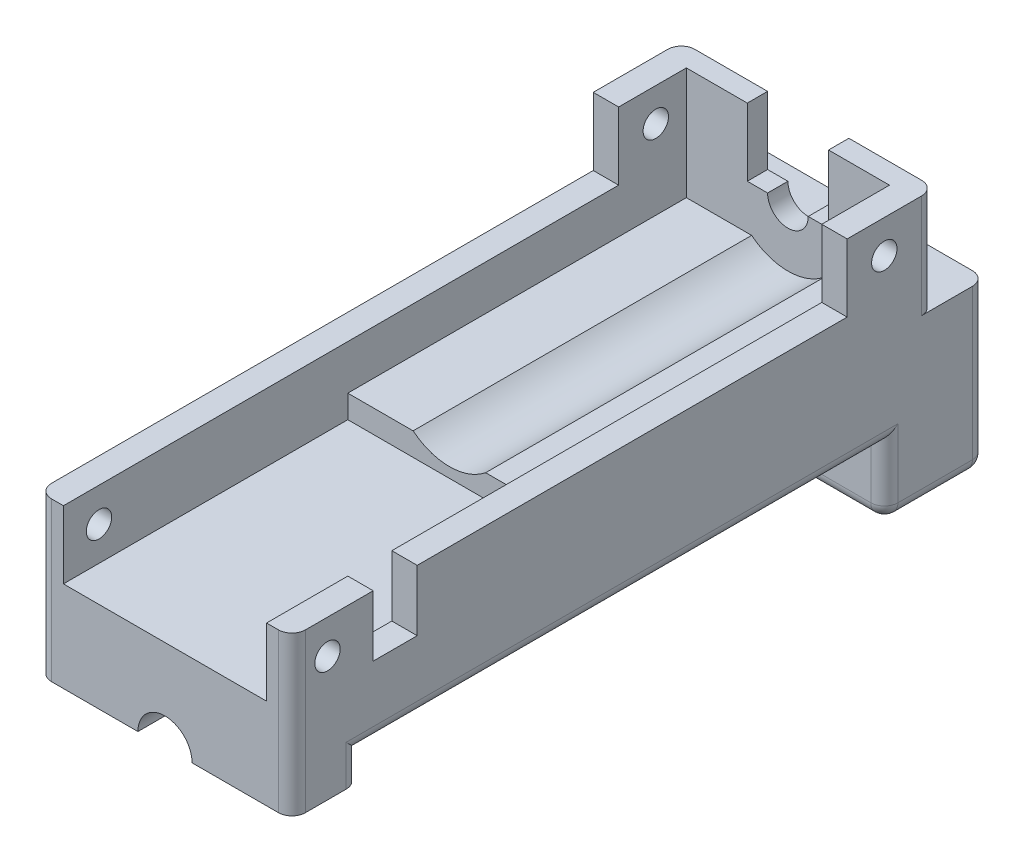
SolidWorks part; units mm, degrees
ref_plane "Front Plane" through (0, 0, 0) normal (0, 0, 1) x (1, 0, 0)
ref_plane "Top Plane" through (0, 0, 0) normal (0, 1, 0) x (1, 0, 0)
ref_plane "Right Plane" through (0, 0, 0) normal (1, 0, 0) x (0, 0, -1)
sketch "Sketch2" plane through (0, 0, 0) normal (0, 1, 0) x (1, 0, 0)
  line L1 (0, 0) -> (37.5, 0)
  line L2 (0, 0) -> (0, 95)
  line L3 (0, 95) -> (37.5, 95)
  line L4 (37.5, 0) -> (37.5, 95)
  dimension "D1" = 37.5
  dimension "D2" = 95
extrude "Boss-Extrude1" add sketch "Sketch2" along normal blind 15
sketch "Sketch3" plane through (0, 15, 0) normal (0, 1, 0) x (1, 0, 0)
  line L0 (0, 0) -> (37.5, 0) construction
  line L1 (3.75, 0) -> (33.75, 0)
  line L2 (3.75, 0) -> (3.75, 42)
  line L3 (3.75, 42) -> (33.75, 42)
  line L4 (33.75, 0) -> (33.75, 42)
  point P4 (18.75, 0)
  point P7 (18.75, 0)
  dimension "D1" = 30
  dimension "D2" = 0
  dimension "D3" = 42
extrude "Cut-Extrude1" cut sketch "Sketch3" against normal blind 10
sketch "Sketch5" plane through (0, 0, -42) normal (0, 0, 1) x (1, 0, 0)
  line L0 (33.75, 5) -> (33.75, 15) construction
  line L1 (3.75, 15) -> (33.75, 15)
  line L2 (3.75, 15) -> (3.75, 8.4)
  line L3 (3.75, 8.4) -> (33.75, 8.4)
  line L4 (33.75, 15) -> (33.75, 8.4)
  line L6 (33.75, 5) -> (3.75, 5) construction
  line L7 (33.75, 15) -> (3.75, 15) construction
  circle A0 centre (18.75, 15) radius 8.5
  line M8 (3.75, 5) -> (33.75, 5)
  dimension "D3" = 17
  dimension "D1" = 0
  dimension "D2" = 3.4
extrude "Cut-Extrude2" cut sketch "Sketch5" against normal blind 50 contours A0 L3 M8 | A0 M8 | A0 L2 L3 M8 | L3 A0 | A0 L3 L4 M8
sketch "Sketch6" plane through (0, 0, -95) normal (0, 0, -1) x (-1, 0, 0)
  line L0 (-37.5, 15) -> (0, 15) construction
  line L1 (-21.75, 15) -> (-15.75, 15)
  arc A0 (-15.75, 15) -> (-21.75, 15) centre (-18.75, 15) cw
  dimension "D1" = 3
extrude "Cut-Extrude3" cut sketch "Sketch6" against normal blind 10
chamfer "Chamfer1" [suppressed] distance 2 angle 45
sketch "Sketch7" plane through (37.5, 0, 0) normal (-1, 0, 0) x (0, 0, 1)
  line L0 (-95, 15) -> (0, 15) construction
  line L1 (-12, 15) -> (-18.5, 15)
  line L2 (-12, 15) -> (-12, 6)
  line L3 (-12, 6) -> (-18.5, 6)
  line L4 (-18.5, 15) -> (-18.5, 6)
  line L5 (-95, 15) -> (-95, 0) construction
  dimension "D1" = 76.5
  dimension "D2" = 6.5
  dimension "D3" = 9
extrude "Cut-Extrude4" cut sketch "Sketch7" against normal up to surface (33.75 mm away)
ref_plane "Plane1" through (18.75, 0, 0) normal (-1, 0, 0) x (0, 0, 1)
sketch "Sketch8" plane through (0, 15, 0) normal (0, 1, 0) x (1, 0, 0)
  line L0 (15.75, 92) -> (3.75, 92) construction
  line L1 (0, 92) -> (12.75, 92)
  line L2 (0, 92) -> (0, 95)
  line L3 (0, 95) -> (12.75, 95)
  line L4 (12.75, 92) -> (12.75, 95)
  line L5 (15.75, 95) -> (0, 95) construction
  line L6 (0, 95) -> (0, 0) construction
  line L7 (15.75, 92) -> (15.75, 95) construction
  dimension "D1" = 0
  dimension "D2" = 3
extrude "Boss-Extrude2" add sketch "Sketch8" along normal blind 10
sketch "Sketch9" plane through (0, 0, -95) normal (0, 0, -1) x (-1, 0, 0)
  line L0 (-12.75, 21.2385) -> (0, 21.2385) construction
  line L1 (-12.75, 25) -> (-12.75, 15) construction
  line L2 (0, 25) -> (0, 0) construction
  point P7 (-7.9314, 21.2385)
hole_wizard "Ø2.5mm Dowel Hole1" [suppressed] positions "Sketch10" profile "Sketch11" hole size "Ø2.5" standard "ANSI Metric"
sketch "Sketch10" plane through (0, 0, -95) normal (0, 0, -1) x (-1, 0, 0)
  point P3 (-7.5318, 21.5512)
sketch "Sketch11" plane through (7.5318, 21.5512, -95) normal (1, 0, 0) x (0, 1, 0)
  line L0 (0, 0) -> (0, 3.9013)
  line L1 (0, 3.9013) -> (1.5, 3)
  line L2 (1.5, 3) -> (1.5, 0)
  line L5 (1.5, 0) -> (0, 0)
  line L10 (0, 3.9013) -> (-1.5, 3) construction
  line L11 (0, -6.35) -> (0, 107.95) construction
  dimension "Hole Dia." = 3
  dimension "Hole Depth" = 3
  dimension "Drill Angle" = 118
mirror "Mirror1" about plane through (18.75, 0, 0) normal (-1, 0, 0) of "Boss-Extrude2", "Ø2.5mm Dowel Hole1"
hole_wizard "Ø2.5mm Dowel Hole2" positions "Sketch12" profile "Sketch13" hole size "Ø2.5" standard "ANSI Metric" end condition through all
sketch "Sketch12" plane through (37.5, 0, 0) normal (1, 0, 0) x (0, 0, -1)
  line L0 (0, 15) -> (0, 0) construction
  line L1 (0, 15) -> (12, 15) construction
  point P0 (5.25, 10)
  dimension "D1" = 5.25
  dimension "D2" = 5
sketch "Sketch13" plane through (37.5, 10, -5.25) normal (0, 1, 0) x (0, 0, -1)
  line L0 (0, 0) -> (0, 37.5)
  line L1 (0, 37.5) -> (1.875, 37.5)
  line L2 (1.875, 37.5) -> (1.875, 0)
  line L5 (1.875, 0) -> (0, 0)
  line L11 (0, -6.35) -> (0, 107.95) construction
  dimension "Thru Hole Dia." = 3.75
  dimension "Thru Hole Depth" = 37.5
sketch "Sketch14" plane through (0, 0, 0) normal (0, -1, 0) x (1, 0, 0)
  line L0 (37.5, 0) -> (37.5, -95) construction
  line L1 (0, -102.5) -> (37.5, -102.5)
  line L2 (0, -102.5) -> (0, -87.5)
  line L3 (0, -87.5) -> (37.5, -87.5)
  line L4 (37.5, -102.5) -> (37.5, -87.5)
  line L5 (37.5, -95) -> (0, -95) construction
  dimension "D1" = 7.5
  dimension "D2" = 15
extrude "Boss-Extrude3" add sketch "Sketch14" along normal blind 14.5
sketch "Sketch15" plane through (0, -14.5, 0) normal (0, -1, 0) x (1, 0, 0)
  line L0 (16.1435, -102.5) -> (16.1435, -100)
  line L1 (0, -102.5) -> (37.5, -102.5) construction
  line L2 (16.1435, -100) -> (12.0031, -100)
  line L3 (12.0031, -100) -> (12.0031, -96.3125)
  line L4 (12.0031, -96.3125) -> (14.305, -96.3125)
  line L5 (14.305, -96.3125) -> (14.305, -87.5)
  line L6 (37.5, -87.5) -> (0, -87.5) construction
  line L7 (14.305, -87.5) -> (23.195, -87.5)
  line L8 (37.5, -87.5) -> (0, -87.5) construction
  line L9 (23.195, -87.5) -> (23.195, -96.3125)
  line L10 (23.195, -96.3125) -> (25.4969, -96.3125)
  line L11 (25.4969, -96.3125) -> (25.4969, -100)
  line L12 (25.4969, -100) -> (21.3565, -100)
  line L13 (21.3565, -100) -> (21.3565, -102.5)
  line L14 (21.3565, -102.5) -> (16.1435, -102.5)
  line L15 (18.75, 19.525) -> (18.75, -19.525) construction
  point P18 (18.75, -102.5)
  dimension "D1" = 2.5
  dimension "D2" = 3.6875
  dimension "D3" = 4.1404
  dimension "D4" = 2.3019
  dimension "D5" = 5.2129
extrude "Cut-Extrude5" cut sketch "Sketch15" against normal blind 11.1125
sketch "Sketch16" plane through (0, -3.3875, 0) normal (0, -1, 0) x (1, 0, 0)
  line L1 (14.305, -87.5) -> (23.195, -87.5)
  line L2 (14.305, -87.5) -> (14.305, -96.3125)
  line L3 (14.305, -96.3125) -> (23.195, -96.3125)
  line L4 (23.195, -87.5) -> (23.195, -96.3125)
extrude "Boss-Extrude4" add sketch "Sketch16" along normal blind 1
fillet "Fillet1" [suppressed] radius 2
sketch "Sketch17" plane through (0, 15, 0) normal (0, 1, 0) x (1, 0, 0)
  line L0 (3.75, 92) -> (3.75, 42) construction
  line L1 (0, 92) -> (3.75, 92)
  line L2 (0, 92) -> (0, 82)
  line L3 (0, 82) -> (3.75, 82)
  line L4 (3.75, 92) -> (3.75, 82)
  line L5 (37.5, 18.5) -> (37.5, 92) construction
  line L6 (33.75, 92) -> (37.5, 92)
  line L7 (33.75, 92) -> (33.75, 82)
  line L8 (33.75, 82) -> (37.5, 82)
  line L9 (37.5, 92) -> (37.5, 82)
  dimension "D1" = 10
extrude "Boss-Extrude5" add sketch "Sketch17" along normal up to surface (10 mm away) up to face at (6.375, 25, -93.5)
sketch "Sketch18" plane through (37.5, 0, 0) normal (1, 0, 0) x (0, 0, -1)
  line L0 (88.5, 25) -> (88.5, 20.1447)
  line L1 (95, 25) -> (82, 25) construction
hole_wizard "Ø2.5mm Dowel Hole3" positions "Sketch19" profile "Sketch20" hole size "Ø2.5" standard "ANSI Metric" end condition through all
sketch "Sketch19" plane through (37.5, 0, 0) normal (1, 0, 0) x (0, 0, -1)
  point P0 (87.4865, 20.1043)
sketch "Sketch20" plane through (37.5, 20.1043, -87.4865) normal (0, 1, 0) x (0, 0, -1)
  line L0 (0, 0) -> (0, 37.5)
  line L1 (0, 37.5) -> (1.875, 37.5)
  line L2 (1.875, 37.5) -> (1.875, 0)
  line L5 (1.875, 0) -> (0, 0)
  line L11 (0, -6.35) -> (0, 107.95) construction
  dimension "Thru Hole Dia." = 3.75
  dimension "Thru Hole Depth" = 37.5
sketch "Sketch21" [suppressed] plane through (0, 0, 0) normal (0, -1, 0) x (1, 0, 0)
  line L0 (32, -2) -> (2, -2) construction
  line L1 (12, -2) -> (22, -2)
  line L2 (12, -2) -> (12, -7)
  line L3 (12, -7) -> (22, -7)
  line L4 (22, -2) -> (22, -7)
  point P6 (17, -2)
  point P7 (17, -7)
  dimension "D1" = 10
  dimension "D2" = 5
extrude "Boss-Extrude6" [suppressed] add sketch "Sketch21" along normal blind 7.5
sketch "Sketch24" plane through (0, 0, -87.5) normal (0, 0, 1) x (1, 0, 0)
  line L0 (37.5, -14.5) -> (37.5, 0) construction
  line L1 (0, 0) -> (37.5, 0)
  line L2 (0, 0) -> (0, -4.3875)
  line L3 (0, -4.3875) -> (37.5, -4.3875)
  line L4 (37.5, 0) -> (37.5, -4.3875)
  line L5 (23.195, -4.3875) -> (14.305, -4.3875) construction
  dimension "D1" = 0
extrude "Boss-Extrude7" add sketch "Sketch24" along normal up to surface (87.5 mm away) up to face at (18.75, 8.75, 0)
sketch "Sketch25" plane through (0, 0, 0) normal (0, 0, 1) x (1, 0, 0)
  line L0 (37.5, -14.5) -> (37.5, -4.3875) construction
  line L1 (0, -4.3875) -> (37.5, -4.3875)
  line L2 (0, -4.3875) -> (0, -8.3875)
  line L3 (0, -8.3875) -> (37.5, -8.3875)
  line L4 (37.5, -4.3875) -> (37.5, -8.3875)
  circle A0 centre (18.75, -8.3875) radius 4
  line M7 (0, -4.3875) -> (37.5, -4.3875)
  dimension "D2" = 8
  dimension "D1" = 4
extrude "Boss-Extrude8" add sketch "Sketch25" against normal blind 10 contours A0 L3 L4 L1 | A0 L2 L3 M7
sketch "Sketch26" plane through (0, 0, -95) normal (0, 0, -1) x (-1, 0, 0)
  line L0 (-37.5, 25) -> (-37.5, 0) construction
  line L1 (-37.5, 9.6903) -> (0, 9.6903)
  line L2 (-37.5, 9.6903) -> (-37.5, 0)
  line L3 (-37.5, 0) -> (0, 0)
  line L4 (0, 9.6903) -> (0, 0)
extrude "Boss-Extrude9" add sketch "Sketch26" along normal up to surface (7.5 mm away) up to face at (18.75, -8.0969, -102.5)
sketch "Sketch27" plane through (0, 0, -102.5) normal (0, 0, -1) x (-1, 0, 0)
  line L0 (0, -14.5) -> (0, 9.6903) construction
  line L1 (-23.05, 6.1903) -> (-3, 6.1903)
  line L2 (-23.05, 6.1903) -> (-23.05, -0.2097)
  line L3 (-23.05, -0.2097) -> (-3, -0.2097)
  line L4 (-3, 6.1903) -> (-3, -0.2097)
  line L5 (-37.5, 9.6903) -> (0, 9.6903) construction
  dimension "D1" = 20.05
  dimension "D2" = 3
  dimension "D3" = 6.4
  dimension "D4" = 3.5
extrude "Cut-Extrude6" cut sketch "Sketch27" against normal blind 14.6
fillet "Fillet2" radius 2 18 edges at (0, 17.3451, -95) (37.5, 17.3451, -95) (0, -2.4049, -102.5) (37.5, -2.4049, -102.5) (37.5, 3.3063, 0) (0, 3.3063, 0) (37.5, -14.5, -95) (37.5, -4.3875, -48.75) (0, -4.3875, -48.75) (0, -14.5, -95) (0, -9.4438, -87.5) (37.5, -9.4438, -87.5) (37.5, -6.3875, -10) (0, -6.3875, -10) (7.1525, -14.5, -87.5) (8.0718, -14.5, -102.5) (29.4282, -14.5, -102.5) (30.3475, -14.5, -87.5)
sketch "Sketch28" plane through (0, -8.3875, 0) normal (0, -1, 0) x (1, 0, 0)
  line L0 (0, -5) -> (5, -5)
  line L1 (0, -8) -> (0, -2) construction
  line L2 (5, -5) -> (32.5, -5)
  line L3 (32.5, -5) -> (37.5, -5)
  line L4 (37.5, -8) -> (37.5, -2) construction
  point P9 (5, -5)
  point P10 (32.5, -5)
  dimension "D1" = 5
  dimension "D2" = 5
hole_wizard "Ø2.5mm Dowel Hole4" positions "Sketch29" profile "Sketch30" hole size "Ø2.5" standard "ANSI Metric"
sketch "Sketch29" plane through (0, -8.3875, 0) normal (0, -1, 0) x (-1, 0, 0)
  point P0 (-32.5, 5)
  point P3 (-5, 5)
sketch "Sketch30" plane through (32.5, -8.3875, -5) normal (1, 0, 0) x (0, 0, -1)
  line L0 (0, 0) -> (0, 6.6524)
  line L1 (0, 6.6524) -> (2.75, 5)
  line L2 (2.75, 5) -> (2.75, 0)
  line L5 (2.75, 0) -> (0, 0)
  line L10 (0, 6.6524) -> (-2.75, 5) construction
  line L11 (0, -6.35) -> (0, 107.95) construction
  dimension "Hole Dia." = 5.5
  dimension "Hole Depth" = 5
  dimension "Drill Angle" = 118
sketch "Sketch31" plane through (3, 0, 0) normal (1, 0, 0) x (0, 0, -1)
  line L0 (87.9, -0.2097) -> (102.5, -0.2097) construction
  line L1 (87.9, 6.1903) -> (92.1849, 6.1903)
  line L2 (87.9, 6.1903) -> (87.9, -0.2097)
  line L3 (87.9, -0.2097) -> (92.1849, -0.2097)
  line L4 (92.1849, 6.1903) -> (92.1849, -0.2097)
extrude "Cut-Extrude7" cut sketch "Sketch31" against normal through all
sketch "Sketch32" plane through (0, -4.3875, 0) normal (0, -1, 0) x (1, 0, 0)
  line L6 (-334.5742, -143.744) -> (-288.4405, 7.0351) construction
  line L7 (32.6622, -66.7314) -> (32.6622, -60.8428)
  line L9 (32.6622, -60.8428) -> (31.3141, -61.258)
  line L10 (31.3141, -61.258) -> (31.3141, -51.0614)
  line L11 (31.3141, -51.0614) -> (31.181, -49.0828)
  line L12 (31.181, -49.0828) -> (30.74, -47.651)
  line L13 (30.74, -47.651) -> (30.2729, -46.7026)
  line L14 (30.2729, -46.7026) -> (29.3435, -45.8252)
  line L15 (29.3435, -45.8252) -> (28.1666, -45.2896)
  line L16 (28.1666, -45.2896) -> (26.913, -45.1722)
  line L17 (26.913, -45.1722) -> (25.4879, -45.4159)
  line L18 (25.4879, -45.4159) -> (23.6632, -46.1151)
  line L19 (23.6632, -46.1151) -> (22.1231, -47.0244)
  line L20 (22.1231, -47.0244) -> (21.2101, -47.821)
  line L21 (21.2101, -47.821) -> (20.0189, -49.0828)
  line L22 (20.0189, -49.0828) -> (18.8875, -51.0614)
  line L23 (18.8875, -51.0614) -> (18.2578, -52.9117)
  line L24 (18.2578, -52.9117) -> (17.9122, -55.2317)
  line L25 (17.9122, -55.2317) -> (19.2824, -54.7067)
  line L26 (19.2824, -54.7067) -> (19.2824, -61.5317)
  line L27 (19.2824, -61.5317) -> (17.8632, -62.0755)
  line L28 (17.8632, -62.0755) -> (17.8632, -66.3603)
  line L29 (17.8632, -66.3603) -> (16.4087, -66.9177)
  line L30 (16.4087, -66.9177) -> (16.4087, -72.6853)
  line L31 (16.4087, -72.6853) -> (23.1935, -70.3053)
  line L32 (23.1935, -70.3053) -> (23.1935, -54.3476)
  line L33 (23.1935, -54.3476) -> (23.331, -53.4242)
  line L34 (23.331, -53.4242) -> (23.5904, -52.662)
  line L35 (23.5904, -52.662) -> (24.1156, -52.1057)
  line L36 (24.1156, -52.1057) -> (24.9501, -51.8129)
  line L37 (24.9501, -51.8129) -> (25.7283, -52.0778)
  line L38 (25.7283, -52.0778) -> (25.9676, -52.76)
  line L39 (25.9676, -52.76) -> (25.9676, -69.1907)
  line L41 (25.9676, -69.1907) -> (32.6622, -66.7314)
  line L42 (18.8875, -61.258) -> (18.8875, -55.3769)
  line L43 (18.8875, -55.3769) -> (17.3894, -55.9273)
  line L44 (17.3894, -55.9273) -> (17.3894, -43.8062)
  line L45 (17.3894, -43.8062) -> (18.8875, -43.2558)
  line L46 (18.8875, -43.2558) -> (18.8875, -37.4484)
  line L47 (18.8875, -37.4484) -> (13.4058, -39.3713)
  line L48 (13.4058, -39.3713) -> (11.1777, -40.3417)
  line L49 (11.1777, -40.3417) -> (10.1006, -40.9833)
  line L50 (10.1006, -40.9833) -> (8.9367, -41.8495)
  line L51 (8.9367, -41.8495) -> (7.791, -42.9514)
  line L52 (7.791, -42.9514) -> (6.7835, -44.1281)
  line L53 (6.7835, -44.1281) -> (6.0815, -45.2896)
  line L54 (6.0815, -45.2896) -> (5.2704, -47.0973)
  line L55 (5.2704, -47.0973) -> (4.8089, -48.4788)
  line L56 (4.8089, -48.4788) -> (4.2957, -50.414)
  line L57 (4.2957, -50.414) -> (4.0218, -53.2385)
  line L58 (4.0218, -53.2385) -> (4.0218, -56.8338)
  line L59 (4.0218, -56.8338) -> (4.2957, -58.8624)
  line L60 (4.2957, -58.8624) -> (4.8089, -60.5277)
  line L61 (4.8089, -60.5277) -> (5.3816, -61.8427)
  line L62 (5.3816, -61.8427) -> (6.3487, -62.8483)
  line L63 (6.3487, -62.8483) -> (7.791, -63.8862)
  line L64 (7.791, -63.8862) -> (9.143, -64.2446)
  line L65 (9.143, -64.2446) -> (10.6392, -64.2446)
  line L66 (10.6392, -64.2446) -> (11.9742, -63.8862)
  line L67 (11.9742, -63.8862) -> (18.8875, -61.258)
  line L68 (12.1359, -57.8481) -> (12.1359, -45.6797)
  line L69 (12.1359, -45.6797) -> (11.3067, -46.2968)
  line L70 (11.3067, -46.2968) -> (10.5406, -47.1916)
  line L71 (10.5406, -47.1916) -> (9.9994, -48.2848)
  line L72 (9.9994, -48.2848) -> (9.6422, -49.6318)
  line L73 (9.6422, -49.6318) -> (9.3926, -51.1318)
  line L74 (9.3926, -51.1318) -> (9.3303, -52.8336)
  line L75 (9.3303, -52.8336) -> (9.3926, -54.2277)
  line L76 (9.3926, -54.2277) -> (9.5692, -55.5356)
  line L77 (9.5692, -55.5356) -> (9.8208, -56.4726)
  line L78 (9.8208, -56.4726) -> (10.3387, -57.4706)
  line L79 (10.3387, -57.4706) -> (10.9236, -57.9715)
  line L80 (10.9236, -57.9715) -> (11.5543, -57.9715)
  line L81 (11.5543, -57.9715) -> (12.1359, -57.8481)
extrude "Cut-Extrude8" cut sketch "Sketch32" against normal blind 1.5
